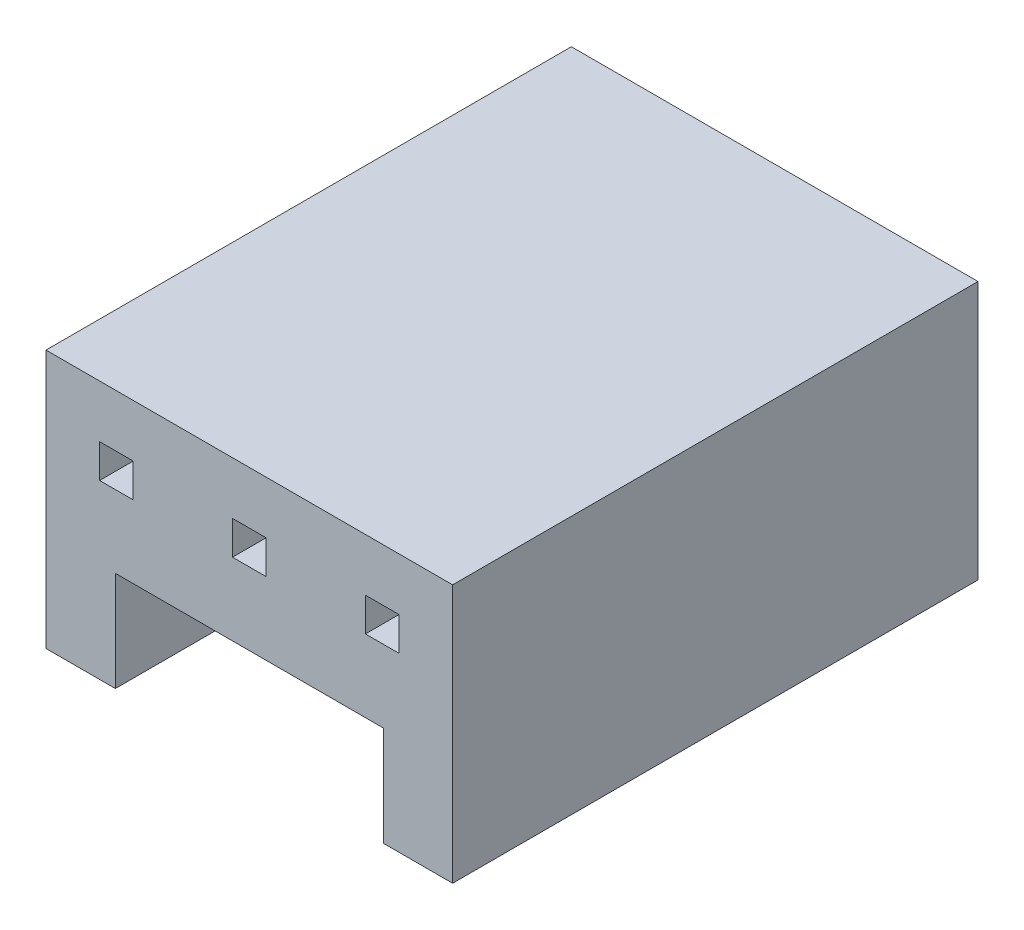
SolidWorks part; units mm, degrees
ref_plane "Front Plane" through (0, 0, 0) normal (0, 0, 1) x (1, 0, 0)
ref_plane "Top Plane" through (0, 0, 0) normal (0, 1, 0) x (1, 0, 0)
ref_plane "Right Plane" through (0, 0, 0) normal (1, 0, 0) x (0, 0, -1)
sketch "Sketch1" plane through (0, 0, 0) normal (0, 0, 1) x (1, 0, 0)
  line L1 (0, 0) -> (7.74, 0)
  line L2 (0, 0) -> (0, 4.92)
  line L3 (0, 4.92) -> (7.74, 4.92)
  line L4 (7.74, 0) -> (7.74, 4.92)
  dimension "D1" = 4.92
  dimension "D2" = 7.74
extrude "Boss-Extrude1" add sketch "Sketch1" against normal blind 10
sketch "Sketch2" plane through (0, 0, 0) normal (0, 0, 1) x (1, 0, 0)
  line L0 (0, 0) -> (7.74, 0) construction
  line L2 (1.32, 0) -> (1.32, 1.9)
  line L3 (1.32, 1.9) -> (6.42, 1.9)
  line L4 (6.42, 0) -> (6.42, 1.9)
  line L5 (1.1448, -2.0305) -> (6.42, 1.9) construction
  line L6 (1.32, 1.9) -> (6.5098, -1.9669) construction
  line L7 (1.32, 0) -> (6.42, 0)
  line L8 (7.74, 4.92) -> (0, 4.92) construction
  line L9 (3.87, 4.92) -> (3.87, -1.12) construction
  point P0 (3.87, 0)
  point P9 (3.87, 1.9)
  dimension "D1" = 5.1
  dimension "D2" = 1.9
extrude "Cut-Extrude1" cut sketch "Sketch2" against normal through all
sketch "Sketch3" plane through (0, 0, 0) normal (0, 0, 1) x (1, 0, 0)
  line L0 (0, 3.6) -> (7.74, 3.6) construction
  line L1 (0, 4.92) -> (0, 0) construction
  line L2 (7.74, 0) -> (7.74, 4.92) construction
  line L3 (1.34, 4.92) -> (1.34, 1.9) construction
  line L4 (7.74, 4.92) -> (0, 4.92) construction
  line L5 (6.42, 1.9) -> (1.32, 1.9) construction
  line L6 (3.87, 4.92) -> (3.87, 1.9) construction
  line L7 (5.8924, 4.92) -> (5.8924, 1.9) construction
  line L8 (3.87, 3.92) -> (3.87, 3.28)
  line L9 (1.02, 3.28) -> (1.66, 3.28)
  line L10 (1.02, 3.28) -> (1.02, 3.92)
  line L11 (1.02, 3.92) -> (1.66, 3.92)
  line L12 (1.66, 3.28) -> (1.66, 3.92)
  line L13 (1.02, 3.28) -> (1.66, 3.92) construction
  line L14 (1.02, 3.92) -> (1.66, 3.28) construction
  line L15 (3.55, 3.28) -> (3.87, 3.28)
  line L16 (3.55, 3.28) -> (3.55, 3.92)
  line L17 (3.55, 3.92) -> (3.87, 3.92)
  line L19 (3.55, 3.28) -> (4.19, 3.92) construction
  line L20 (3.55, 3.92) -> (4.19, 3.28) construction
  point P16 (1.34, 3.6)
  point P22 (3.87, 3.6)
  dimension "D1" = 0.64
  dimension "D2" = 0.64
  dimension "D3" = 1.34
  dimension "D4" = 1.32
  dimension "D5" = 0.64
  dimension "D6" = 0.64
extrude "Cut-Extrude2" cut sketch "Sketch3" against normal through all
ref_plane "Plane1" through (3.87, 0, 0) normal (-1, 0, 0) x (0, 0, 1)
mirror "Mirror1" about plane through (3.87, 0, 0) normal (-1, 0, 0) of "Cut-Extrude2"
